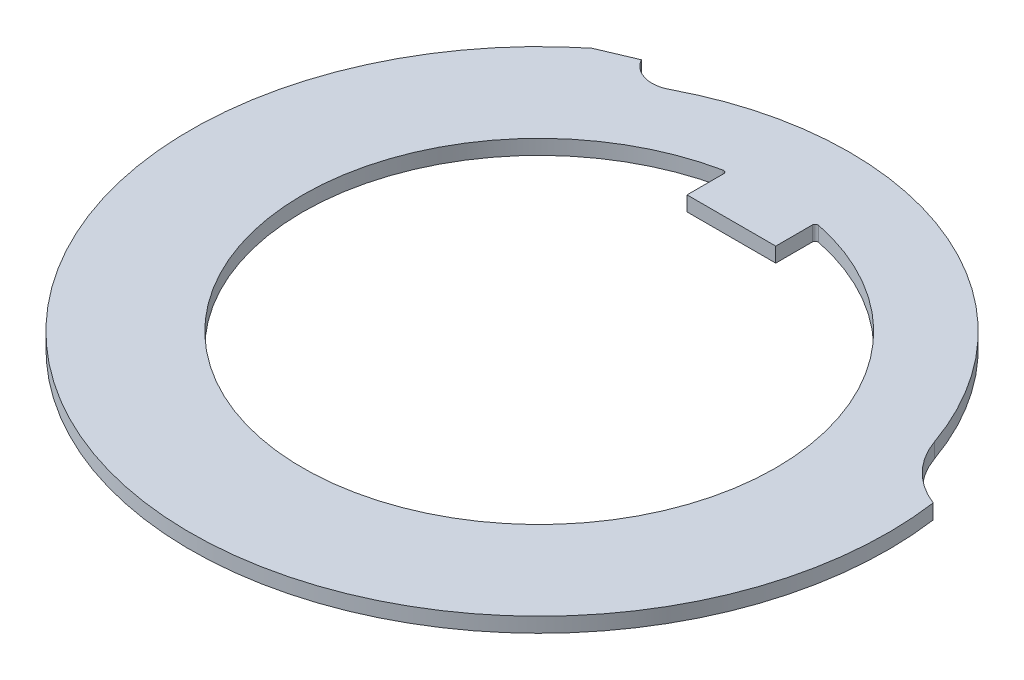
SolidWorks part; units mm, degrees
ref_plane "Front Plane" through (0, 0, 0) normal (0, 0, 1) x (1, 0, 0)
ref_plane "Top Plane" through (0, 0, 0) normal (0, 1, 0) x (1, 0, 0)
ref_plane "Right Plane" through (0, 0, 0) normal (1, 0, 0) x (0, 0, -1)
sketch "Sketch1" plane through (0, 0, 0) normal (0, 1, 0) x (1, 0, 0)
  line L0 (0, 11.8) -> (0, -10.5) construction
  line L1 (-6.23, 9.6857) -> (0, 0) construction
  line L2 (0, 0) -> (11.6852, 1.6422) construction
  line L4 (-7.4058, 9.1866) -> (-6.23, 9.6857)
  line L5 (0, 0) -> (11.8, 0) construction
  line L6 (-1.5, 6.5) -> (1.5, 6.5)
  line L7 (-1.5, 6.5) -> (-1.5, 7.8581)
  line L9 (1.5, 6.5) -> (1.5, 7.8581)
  line L10 (-1.5, 6.5) -> (0, 8) construction
  line L11 (0, 8) -> (1.5, 6.5) construction
  arc A0 (-11.0527, -4.1324) -> (11.6852, 1.6422) centre (0, 0) ccw
  arc A1 (-1.5, 7.8581) -> (1.5, 7.8581) centre (0, 0) ccw
  arc A5 (9.9136, 3.4599) -> (-4.8923, 9.2906) centre (0, 0) ccw
  arc A6 (-4.8923, 9.2906) -> (-6.23, 9.6857) centre (-5.3582, 10.1755) cw
  arc A7 (11.6852, 1.6422) -> (9.9136, 3.4599) centre (12.746, 4.4484) cw
  arc A8 (-7.4058, 9.1866) -> (-11.0527, -4.1324) centre (0, 0) ccw
  point P4 (0, 8)
  point P27 (0, 0)
  dimension "D1" = 23.6
  dimension "D2" = 16
  dimension "D3" = 32.75
  dimension "D6" = 3
  dimension "D7" = 23
  dimension "D5" = 10.5
  dimension "D9" = 1
  dimension "D4" = 114.75
  dimension "D8" = 11.35
  dimension "D10" = 6.5
  dimension "D11" = 3
extrude "Boss-Extrude1" add sketch "Sketch1" along normal blind 0.5
fillet "Fillet1" radius 0.1 2 edges at (-1.5, 0.25, -7.8581) (1.5, 0.25, -7.8581)
